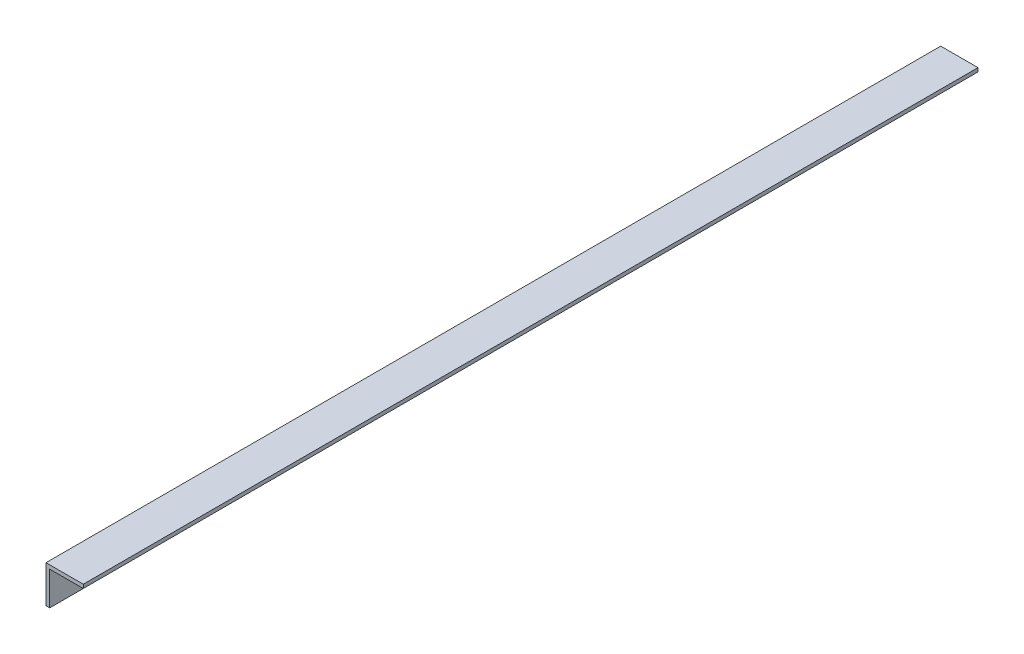
SolidWorks part; units mm, degrees
ref_plane "Спереди" through (0, 0, 0) normal (0, 0, 1) x (1, 0, 0)
ref_plane "Сверху" through (0, 0, 0) normal (0, 1, 0) x (1, 0, 0)
ref_plane "Справа" through (0, 0, 0) normal (1, 0, 0) x (0, 0, -1)
sketch "Эскиз1" plane through (0, 0, 0) normal (0, 0, 1) x (1, 0, 0)
  line L0 (0, 0) -> (0, -50)
  line L1 (0, 0) -> (50, 0)
extrude "Вытянуть-Тонкостенный1" add sketch "Эскиз1" against normal blind 1200 thin thin type one direction wall 5
